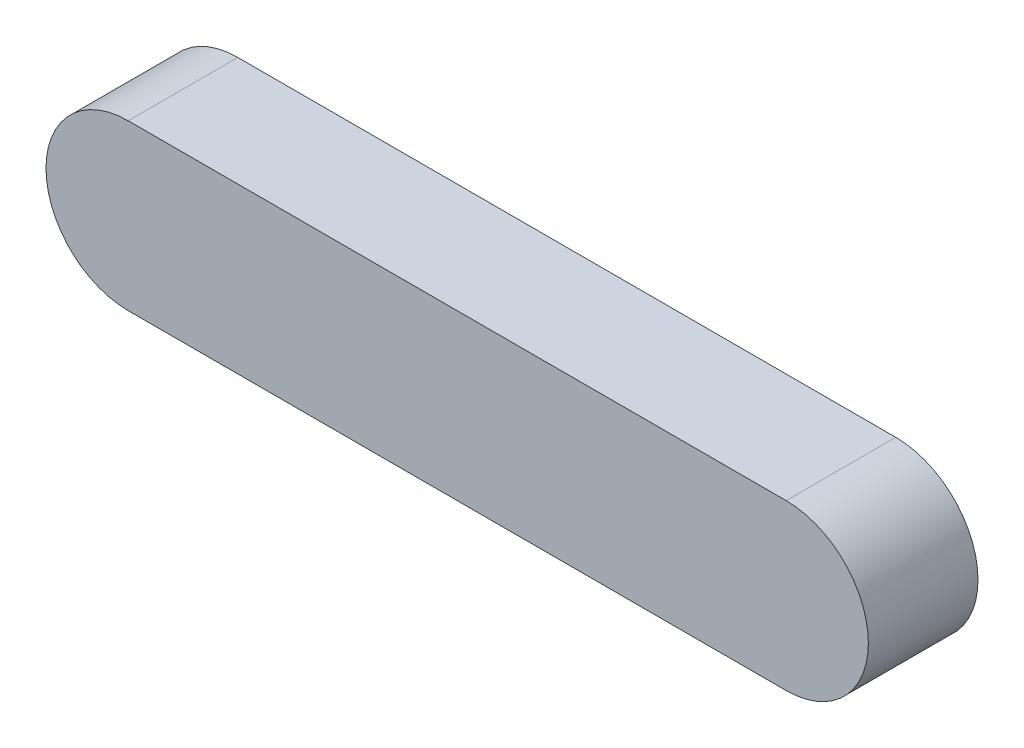
SolidWorks part; units mm, degrees
ref_plane "前视基准面" through (0, 0, 0) normal (0, 0, 1) x (1, 0, 0)
ref_plane "上视基准面" through (0, 0, 0) normal (0, 1, 0) x (1, 0, 0)
ref_plane "右视基准面" through (0, 0, 0) normal (1, 0, 0) x (0, 0, -1)
sketch "草图1" plane through (0, 0, 0) normal (0, 0, 1) x (1, 0, 0)
  line L0 (0, 0) -> (-60, 0) construction
  line L1 (0, -7.5) -> (-60, -7.5)
  line L2 (0, 7.5) -> (-60, 7.5)
  arc A0 (0, -7.5) -> (0, 7.5) centre (0, 0) ccw
  arc A1 (-60, 7.5) -> (-60, -7.5) centre (-60, 0) ccw
  point P2 (-30, 0)
  dimension "D1" = 60
  dimension "D2" = 15
extrude "凸台-拉伸1" add sketch "草图1" along normal blind 10
